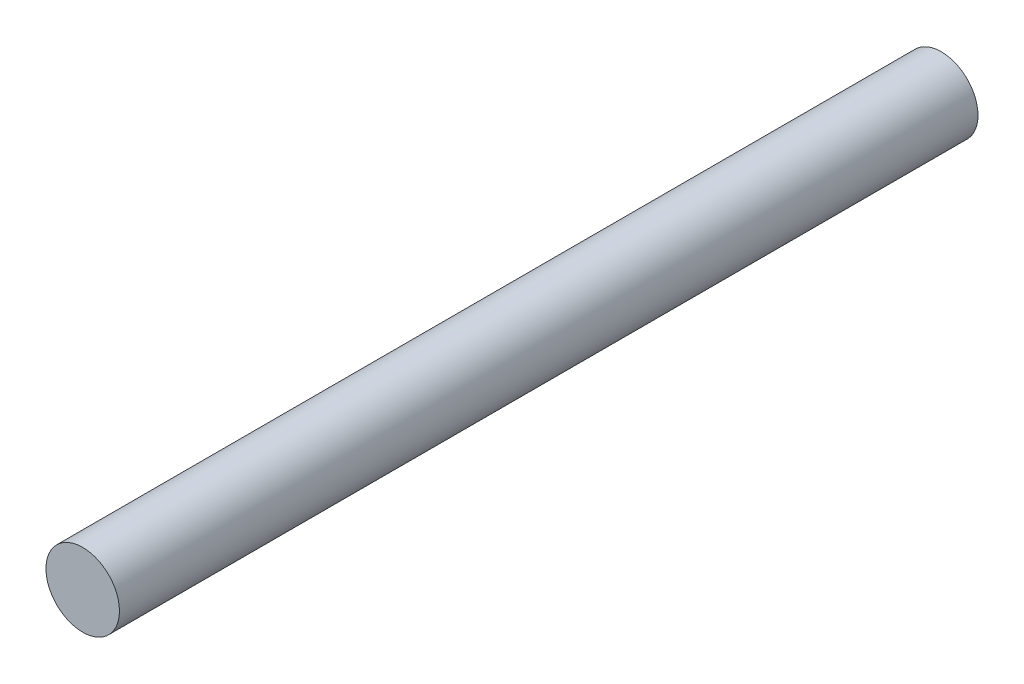
SolidWorks part; units mm, degrees
ref_plane "Front Plane" through (0, 0, 0) normal (0, 0, 1) x (1, 0, 0)
ref_plane "Top Plane" through (0, 0, 0) normal (0, 1, 0) x (1, 0, 0)
ref_plane "Right Plane" through (0, 0, 0) normal (1, 0, 0) x (0, 0, -1)
sketch "Sketch1" plane through (0, 0, 0) normal (0, 0, 1) x (1, 0, 0)
  circle A0 centre (0, 0) radius 2.3813
  dimension "D1" = 4.7625
extrude "Boss-Extrude1" add sketch "Sketch1" along normal blind 55.626
